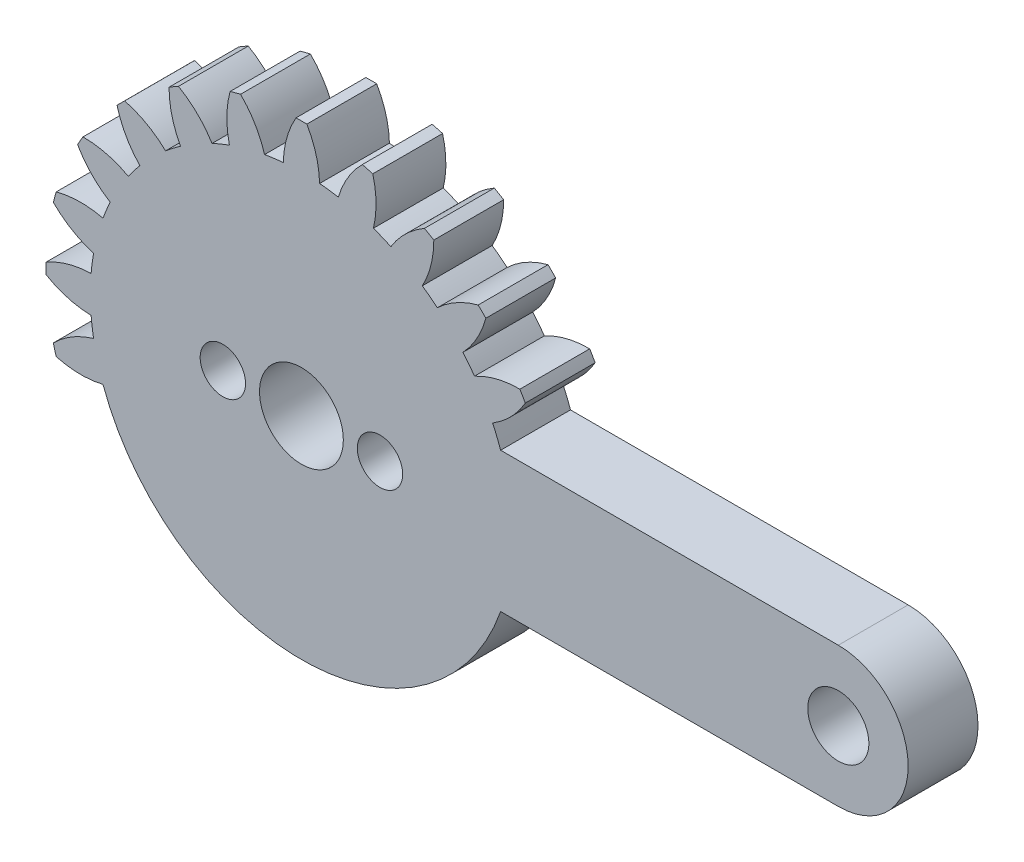
SolidWorks part; units mm, degrees
ref_plane "Plan de face" through (0, 0, 0) normal (0, 0, 1) x (1, 0, 0)
ref_plane "Plan de dessus" through (0, 0, 0) normal (0, 1, 0) x (1, 0, 0)
ref_plane "Plan de droite" through (0, 0, 0) normal (1, 0, 0) x (0, 0, -1)
sketch "Esquisse1" plane through (0, 0, 0) normal (0, 0, 1) x (1, 0, 0)
  line L0 (0, 0) -> (0, 14.63) construction
  line L1 (0, 0) -> (30.75, 0) construction
  line L2 (14.0726, 4) -> (30.75, 4)
  line L3 (11.4091, -4) -> (30.75, -4)
  line L4 (14.0726, 4) -> (11.4091, 4)
  circle A0 centre (0, 0) radius 1.75
  circle A1 centre (0, 0) radius 12.09
  arc A2 (14.0726, -4) -> (14.0726, 4) centre (0, 0) ccw
  arc A3 (-0.31, 14.6267) -> (-1.04, 12.0452) centre (4.3584, 11.9126) ccw
  arc A4 (0.31, 14.6267) -> (1.04, 12.0452) centre (-4.3584, 11.9126) cw
  arc A5 (0.31, 14.6267) -> (-0.31, 14.6267) centre (0, 0) ccw
  arc A6 (4.0851, 14.0481) -> (4.1221, 11.3656) centre (-1.1267, 12.6347) cw
  arc A7 (3.4862, 14.2086) -> (2.113, 11.9039) centre (7.2931, 10.3787) ccw
  arc A8 (4.0851, 14.0481) -> (3.4862, 14.2086) centre (0, 0) ccw
  arc A9 (7.5818, 12.5121) -> (6.9233, 9.9114) centre (2.1819, 12.4958) cw
  arc A10 (7.0449, 12.8221) -> (5.1219, 10.9514) centre (9.7308, 8.1374) ccw
  arc A11 (7.5818, 12.5121) -> (7.0449, 12.8221) centre (0, 0) ccw
  arc A12 (10.5619, 10.1234) -> (9.2526, 7.7818) centre (5.3417, 11.5053) cw
  arc A13 (10.1234, 10.5619) -> (7.7818, 9.2526) centre (11.5053, 5.3417) ccw
  arc A14 (10.5619, 10.1234) -> (10.1234, 10.5619) centre (0, 0) ccw
  arc A15 (12.8221, 7.0449) -> (10.9514, 5.1219) centre (8.1374, 9.7308) cw
  arc A16 (12.5121, 7.5818) -> (9.9114, 6.9233) centre (12.4958, 2.1819) ccw
  arc A17 (12.8221, 7.0449) -> (12.5121, 7.5818) centre (0, 0) ccw
  arc A18 (14.2086, 3.4862) -> (11.9039, 2.113) centre (10.3787, 7.2931) cw
  arc A19 (14.0481, 4.0851) -> (11.3656, 4.1221) centre (12.6347, -1.1267) ccw
  arc A20 (14.2086, 3.4862) -> (14.0481, 4.0851) centre (0, 0) ccw
  arc A21 (14.6267, -0.31) -> (12.0452, -1.04) centre (11.9126, 4.3584) cw
  arc A22 (14.6267, 0.31) -> (12.0452, 1.04) centre (11.9126, -4.3584) ccw
  arc A23 (14.6267, -0.31) -> (14.6267, 0.31) centre (0, 0) ccw
  arc A24 (14.0481, -4.0851) -> (11.3656, -4.1221) centre (12.6347, 1.1267) cw
  arc A25 (14.2086, -3.4862) -> (11.9039, -2.113) centre (10.3787, -7.2931) ccw
  arc A26 (14.0481, -4.0851) -> (14.2086, -3.4862) centre (0, 0) ccw
  arc A27 (12.5121, -7.5818) -> (9.9114, -6.9233) centre (12.4958, -2.1819) cw
  arc A28 (12.8221, -7.0449) -> (10.9514, -5.1219) centre (8.1374, -9.7308) ccw
  arc A29 (12.5121, -7.5818) -> (12.8221, -7.0449) centre (0, 0) ccw
  arc A30 (10.1234, -10.5619) -> (7.7818, -9.2526) centre (11.5053, -5.3417) cw
  arc A31 (10.5619, -10.1234) -> (9.2526, -7.7818) centre (5.3417, -11.5053) ccw
  arc A32 (10.1234, -10.5619) -> (10.5619, -10.1234) centre (0, 0) ccw
  arc A33 (7.0449, -12.8221) -> (5.1219, -10.9514) centre (9.7308, -8.1374) cw
  arc A34 (7.5818, -12.5121) -> (6.9233, -9.9114) centre (2.1819, -12.4958) ccw
  arc A35 (7.0449, -12.8221) -> (7.5818, -12.5121) centre (0, 0) ccw
  arc A36 (3.4862, -14.2086) -> (2.113, -11.9039) centre (7.2931, -10.3787) cw
  arc A37 (4.0851, -14.0481) -> (4.1221, -11.3656) centre (-1.1267, -12.6347) ccw
  arc A38 (3.4862, -14.2086) -> (4.0851, -14.0481) centre (0, 0) ccw
  arc A39 (-0.31, -14.6267) -> (-1.04, -12.0452) centre (4.3584, -11.9126) cw
  arc A40 (0.31, -14.6267) -> (1.04, -12.0452) centre (-4.3584, -11.9126) ccw
  arc A41 (-0.31, -14.6267) -> (0.31, -14.6267) centre (0, 0) ccw
  arc A42 (-4.0851, -14.0481) -> (-4.1221, -11.3656) centre (1.1267, -12.6347) cw
  arc A43 (-3.4862, -14.2086) -> (-2.113, -11.9039) centre (-7.2931, -10.3787) ccw
  arc A44 (-4.0851, -14.0481) -> (-3.4862, -14.2086) centre (0, 0) ccw
  arc A45 (-7.5818, -12.5121) -> (-6.9233, -9.9114) centre (-2.1819, -12.4958) cw
  arc A46 (-7.0449, -12.8221) -> (-5.1219, -10.9514) centre (-9.7308, -8.1374) ccw
  arc A47 (-7.5818, -12.5121) -> (-7.0449, -12.8221) centre (0, 0) ccw
  arc A48 (-10.5619, -10.1234) -> (-9.2526, -7.7818) centre (-5.3417, -11.5053) cw
  arc A49 (-10.1234, -10.5619) -> (-7.7818, -9.2526) centre (-11.5053, -5.3417) ccw
  arc A50 (-10.5619, -10.1234) -> (-10.1234, -10.5619) centre (0, 0) ccw
  arc A51 (30.75, 4) -> (30.75, -4) centre (30.75, 0) cw
  circle A52 centre (30.75, 0) radius 1.75
  arc A56 (-12.8221, -7.0449) -> (-10.9514, -5.1219) centre (-8.1374, -9.7308) cw
  arc A57 (-12.5121, -7.5818) -> (-9.9114, -6.9233) centre (-12.4958, -2.1819) ccw
  arc A58 (-12.8221, -7.0449) -> (-12.5121, -7.5818) centre (0, 0) ccw
  arc A59 (-14.2086, -3.4862) -> (-11.9039, -2.113) centre (-10.3787, -7.2931) cw
  arc A60 (-14.0481, -4.0851) -> (-11.3656, -4.1221) centre (-12.6347, 1.1267) ccw
  arc A61 (-14.2086, -3.4862) -> (-14.0481, -4.0851) centre (0, 0) ccw
  arc A62 (-14.6267, 0.31) -> (-12.0452, 1.04) centre (-11.9126, -4.3584) cw
  arc A63 (-14.6267, -0.31) -> (-12.0452, -1.04) centre (-11.9126, 4.3584) ccw
  arc A64 (-14.6267, 0.31) -> (-14.6267, -0.31) centre (0, 0) ccw
  arc A65 (-14.0481, 4.0851) -> (-11.3656, 4.1221) centre (-12.6347, -1.1267) cw
  arc A66 (-14.2086, 3.4862) -> (-11.9039, 2.113) centre (-10.3787, 7.2931) ccw
  arc A67 (-14.0481, 4.0851) -> (-14.2086, 3.4862) centre (0, 0) ccw
  arc A68 (-12.5121, 7.5818) -> (-9.9114, 6.9233) centre (-12.4958, 2.1819) cw
  arc A69 (-12.8221, 7.0449) -> (-10.9514, 5.1219) centre (-8.1374, 9.7308) ccw
  arc A70 (-12.5121, 7.5818) -> (-12.8221, 7.0449) centre (0, 0) ccw
  arc A71 (-10.1234, 10.5619) -> (-7.7818, 9.2526) centre (-11.5053, 5.3417) cw
  arc A72 (-10.5619, 10.1234) -> (-9.2526, 7.7818) centre (-5.3417, 11.5053) ccw
  arc A73 (-10.1234, 10.5619) -> (-10.5619, 10.1234) centre (0, 0) ccw
  arc A74 (-7.0449, 12.8221) -> (-5.1219, 10.9514) centre (-9.7308, 8.1374) cw
  arc A75 (-7.5818, 12.5121) -> (-6.9233, 9.9114) centre (-2.1819, 12.4958) ccw
  arc A76 (-7.0449, 12.8221) -> (-7.5818, 12.5121) centre (0, 0) ccw
  arc A77 (-3.4862, 14.2086) -> (-2.113, 11.9039) centre (-7.2931, 10.3787) cw
  arc A78 (-4.0851, 14.0481) -> (-4.1221, 11.3656) centre (1.1267, 12.6347) ccw
  arc A79 (-3.4862, 14.2086) -> (-4.0851, 14.0481) centre (0, 0) ccw
  point P152 (0, 0)
  point P171 (0, 0)
  dimension "D1" = 3.5
  dimension "D2" = 24.18
  dimension "D3" = 29.26
  dimension "D6" = 5.4
  dimension "D8" = 4
  dimension "D10" = 3.5
  dimension "D4" = 0.62
  dimension "D5" = 2.08
  dimension "D9" = 30.75
  dimension "D7" = 24
extrude "Boss.-Extru.1" add sketch "Esquisse1" along normal mid plane 4 contours A1 | A51 L2 A2 L3 A52 | A22 A2 A18 A1 | A18 A2 L4 A1 | A2 A25 A1 L3 | A25 A2 A21 A1 | A2 A22 A1 A21 | A15 A17 A16 A1 | A12 A14 A13 A1 | A9 A11 A10 A1 | A6 A8 A7 A1 | A4 A5 A3 A1 | A77 A79 A78 A1 | A74 A76 A75 A1 | A71 A73 A72 A1 | A68 A70 A69 A1 | A65 A67 A66 A1 | A62 A64 A63 A1 | A59 A61 A60 A1
sketch "Esquisse2" plane through (0, 0, 2) normal (0, 0, 1) x (1, 0, 0)
  line L0 (-4.5, 0) -> (4.5, 0) construction
  circle A0 centre (4.5, 0) radius 1.3
  circle A1 centre (-4.5, 0) radius 1.3
  circle A2 centre (0, 0) radius 2.4
  dimension "D1" = 2.6
  dimension "D3" = 4.8
  dimension "D2" = 9
extrude "Enlèv. mat.-Extru.1" cut sketch "Esquisse2" against normal through all both and the other way through all
